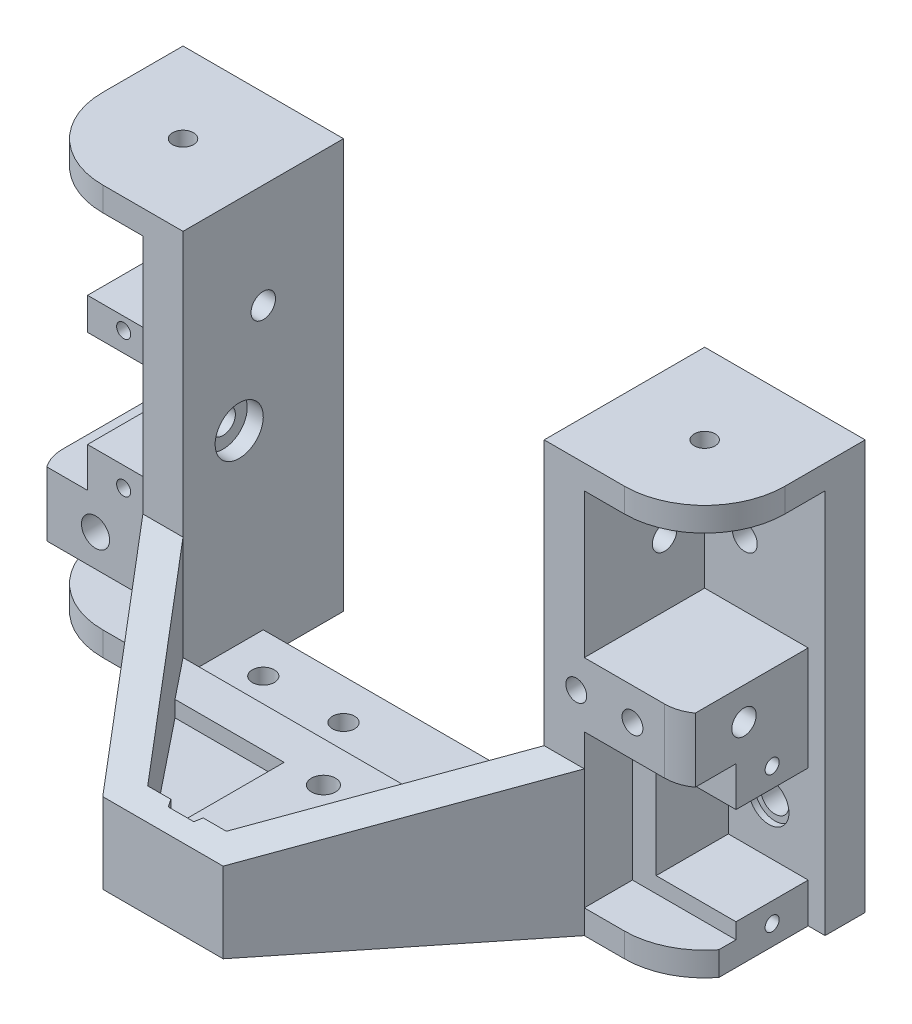
SolidWorks part; units mm, degrees
material "ABS"
ref_plane "Front Plane" through (0, 0, 0) normal (0, 0, 1) x (1, 0, 0)
ref_plane "Top Plane" through (0, 0, 0) normal (0, 1, 0) x (1, 0, 0)
ref_plane "Right Plane" through (0, 0, 0) normal (1, 0, 0) x (0, 0, -1)
sketch "Sketch1" plane through (0, 0, 0) normal (0, 0, 1) x (1, 0, 0)
  line L0 (-22.5, 7) -> (0, 7)
  line L1 (22.5, 7) -> (22.5, 45)
  line L2 (22.5, 45) -> (42.5, 45)
  line L3 (42.5, 45) -> (42.5, 0)
  line L4 (42.5, 0) -> (-42.5, 0)
  line L5 (-42.5, 0) -> (-42.5, 45)
  line L6 (-42.5, 45) -> (-22.5, 45)
  line L7 (-22.5, 45) -> (-22.5, 7)
  line L8 (-35.5, 39.9194) -> (-35.5, 0) construction
  line L9 (35.5, 39.9194) -> (35.5, 0) construction
  line L10 (0, 7) -> (0, 0) construction
  line L14 (0, 7) -> (22.5, 7)
  circle A0 centre (35.5, 8) radius 1.75
  circle A1 centre (-35.5, 8) radius 1.75
  circle A2 centre (32.5, 35) radius 1.55
  circle A3 centre (-32.5, 35) radius 1.55
  point P8 (0, 0)
  dimension "D3" = 3.5
  dimension "D10" = 3.1
  dimension "D1" = 71
  dimension "D2" = 22.5
  dimension "D4" = 8
  dimension "D5" = 7
  dimension "D6" = 7
  dimension "D7" = 45
  dimension "D8" = 35
  dimension "D9" = 3
extrude "main flange" add sketch "Sketch1" along normal blind 5
ref_plane "Plane1" through (22.5, 0, 0) normal (1, 0, 0) x (0, 0, -1)
sketch "Sketch2" plane through (22.5, 0, 0) normal (1, 0, 0) x (0, 0, -1)
  line L0 (-13, 45) -> (-13, 0) construction
  line L1 (-5, 45) -> (-20, 45)
  line L2 (-5, 45) -> (-5, 0)
  line L3 (-5, 0) -> (-20, 0)
  line L4 (-20, 45) -> (-20, 0)
  circle A0 centre (-13, 23) radius 1.525
  circle A1 centre (-10, 35) radius 1.525
  dimension "D2" = 3.05
  dimension "D5" = 3.05
  dimension "D1" = 15
  dimension "D3" = 23
  dimension "D4" = 13
  dimension "D6" = 35
  dimension "D7" = 3
extrude "side flange" add sketch "Sketch2" along normal blind 5
sketch "Sketch8" plane through (22.5, 0, 0) normal (-1, 0, 0) x (0, 0, 1)
  circle A0 centre (13, 23) radius 3
  dimension "D1" = 6
extrude "bearing cutout" [suppressed] cut sketch "Sketch8" against normal blind 2
mirror "Mirror1" about plane through (0, 0, 0) normal (1, 0, 0) of "side flange"
sketch "Sketch11" plane through (0, 0, 0) normal (0, -1, 0) x (1, 0, 0)
  line L0 (27.5, 20) -> (22.5, 20) construction
  line L1 (-42.5, 0) -> (42.5, 0)
  line L2 (-42.5, 0) -> (-42.5, 10)
  line L3 (-32.5, 20) -> (32.5, 20)
  line L4 (42.5, 0) -> (42.5, 10)
  arc A0 (32.5, 20) -> (42.5, 10) centre (32.5, 10) cw
  arc A1 (-42.5, 10) -> (-32.5, 20) centre (-32.5, 10) cw
  circle A2 centre (-32.5, 10) radius 1.3
  circle A3 centre (32.5, 10) radius 1.3
  dimension "D1" = 10
  dimension "D2" = 2.6
extrude "Boss-Extrude3" add sketch "Sketch11" along normal blind 3
sketch "Sketch12" plane through (0, 0, 0) normal (0, 1, 0) x (1, 0, 0)
  line L0 (-4, -3) -> (-4, 0)
  line L1 (22.5, 0) -> (-22.5, 0) construction
  line L2 (-4, 0) -> (4, 0)
  line L3 (4, 0) -> (4, -3)
  line L4 (0, 0) -> (0, -3) construction
  arc A0 (4, -3) -> (-4, -3) centre (0, -3) cw
  circle A1 centre (0, -3) radius 1.5 construction
  dimension "D2" = 8
  dimension "D3" = 3
  dimension "D1" = 3
extrude "Boss-Extrude4" add sketch "Sketch12" along normal up to surface (7 mm away) up to face at (5.625, 7, 3.125)
hole_wizard "CSK for M3 Flat Head Machine Screw1" positions "Sketch14" profile "Sketch15" countersink size "M3" standard "ANSI Metric" end condition up to next
sketch "Sketch14" plane through (0, -3, 0) normal (0, -1, 0) x (-1, 0, 0)
  line L0 (0, -3) -> (0, 0) construction
  point P0 (0, -3)
  dimension "D1" = 3
sketch "Sketch15" plane through (0, -3, 3) normal (1, 0, 0) x (0, 0, -1)
  line L0 (0, 0) -> (0, 10)
  line L1 (0, 10) -> (1.8, 10)
  line L2 (1.8, 10) -> (1.8, 1.5)
  line L3 (1.8, 1.5) -> (3.15, 0.15)
  line L4 (3.15, 0.15) -> (3.15, 0)
  line L6 (3.15, 0) -> (0, 0)
  line L7 (-1.8, 1.5) -> (-3.15, 0.15) construction
  line L11 (0, -6.35) -> (0, 107.95) construction
  dimension "Thru Hole Dia." = 3.6
  dimension "Thru Hole Depth" = 10
  dimension "C'Sink Dia." = 6.3
  dimension "C'Sink Angle" = 90
  dimension "Head Clearance" = 0.15
sketch "Sketch16" plane through (0, 45, 0) normal (0, 1, 0) x (1, 0, 0)
  line L0 (-22.5, 0) -> (-42.5, 0) construction
  line L1 (-42.5, 0) -> (-22.5, 0)
  line L2 (-42.5, 0) -> (-42.5, -10)
  line L3 (-32.5, -20) -> (-22.5, -20)
  line L4 (42.5, 0) -> (42.5, -10)
  line L5 (-42.5, -5) -> (-42.5, 0) construction
  line L6 (42.5, -5) -> (42.5, 0) construction
  line L7 (27.5, -20) -> (22.5, -20) construction
  line L8 (-22.5, 0) -> (-22.5, -20)
  line L9 (-22.5, -20) -> (-22.5, 0) construction
  line L10 (22.5, 0) -> (22.5, -20)
  line L11 (22.5, -20) -> (22.5, 0) construction
  line L12 (22.5, 0) -> (42.5, 0)
  line L13 (22.5, -20) -> (32.5, -20)
  arc A0 (-42.5, -10) -> (-32.5, -20) centre (-32.5, -10) ccw
  arc A1 (32.5, -20) -> (42.5, -10) centre (32.5, -10) ccw
  circle A2 centre (-32.5, -10) radius 1.3
  circle A3 centre (32.5, -10) radius 1.3
  dimension "D1" = 10
  dimension "D2" = 2.6
extrude "Top support" add sketch "Sketch16" along normal blind 3
sketch "Sketch18" plane through (27.5, 0, 0) normal (1, 0, 0) x (0, 0, -1)
  line L0 (-20, 45) -> (-20, 0) construction
  line L1 (-20, 27) -> (-5, 27)
  line L2 (-20, 27) -> (-20, 19)
  line L3 (-20, 19) -> (-5, 19)
  line L4 (-5, 27) -> (-5, 19)
  line L5 (-5, 0) -> (-5, 45) construction
  circle A0 centre (-13, 23) radius 1.525
  circle A1 centre (-13, 23) radius 1.525 construction
  dimension "D1" = 4
  dimension "D2" = 4
extrude "Boss-Extrude5" add sketch "Sketch18" along normal up to surface (15 mm away) up to face at (42.5, 19.6875, 5.9375)
sketch "Sketch19" plane through (0, 0, 5) normal (0, 0, 1) x (1, 0, 0)
  line L0 (-27.5, 45) -> (-27.5, 0) construction
  line L1 (-27.5, 12) -> (-42.5, 12)
  line L2 (-27.5, 12) -> (-27.5, 4)
  line L3 (-27.5, 4) -> (-42.5, 4)
  line L4 (-42.5, 12) -> (-42.5, 4)
  line L5 (-42.5, 45) -> (-42.5, 0) construction
  circle A0 centre (-35.5, 8) radius 1.75
  circle A1 centre (-35.5, 8) radius 1.75 construction
  dimension "D1" = 4
  dimension "D2" = 4
extrude "Boss-Extrude6" add sketch "Sketch19" along normal up to surface (15 mm away) up to face at (8.375, 27.35, 20)
fillet "Fillet1" radius 5 2 edges at (42.5, 23, 20) (-42.5, 8, 20)
hole_wizard "M3x0.5 Tapped Hole1" positions "Sketch21" profile "Sketch20" tap size "M3x0.5" standard "ANSI Metric"
sketch "Sketch21" plane through (-42.5, 0, 0) normal (-1, 0, 0) x (0, 0, 1)
  line L2 (15, 8) -> (4, 8) construction
  line L3 (0, 48) -> (0, -3) construction
  line L5 (15, 4) -> (15, 12) construction
  point P0 (11, 8)
  point P11 (4, 8)
  dimension "D1" = 4
  dimension "D3" = 7
sketch "Sketch20" plane through (-42.5, 8, 11) normal (0, 1, 0) x (0, 0, 1)
  line L0 (0, 0) -> (0, 8.2811)
  line L1 (0, 8.2811) -> (1.3, 7.5)
  line L2 (1.3, 7.5) -> (1.3, 0)
  line L5 (1.3, 0) -> (0, 0)
  line L10 (0, 8.2811) -> (-1.3, 7.5) construction
  line L11 (0, -6.35) -> (0, 107.95) construction
  dimension "Tap Drill Dia." = 2.6
  dimension "Tap Drill Depth" = 7.5
  dimension "Drill Angle" = 118
cosmetic thread "Hole Thread1" parameters "D1"=6, "D2"=3
cosmetic thread "Hole Thread2" parameters "D1"=6, "D2"=3
hole_wizard "M3x0.5 Tapped Hole2" positions "Sketch23" profile "Sketch22" tap size "M3x0.5" standard "ANSI Metric"
sketch "Sketch23" plane through (0, 0, 20) normal (0, 0, 1) x (1, 0, 0)
  line L0 (22.5, 23) -> (33.5, 23) construction
  line L1 (22.5, 48) -> (22.5, 0) construction
  line L5 (33.5, 23) -> (37.5, 23) construction
  line L6 (37.5, 19) -> (37.5, 27) construction
  point P0 (33.5, 23)
  point P2 (26.5, 23)
  dimension "D1" = 4
  dimension "D2" = 7
sketch "Sketch22" plane through (33.5, 23, 20) normal (1, 0, 0) x (0, -1, 0)
  line L0 (0, 0) -> (0, 8.2811)
  line L1 (0, 8.2811) -> (1.3, 7.5)
  line L2 (1.3, 7.5) -> (1.3, 0)
  line L5 (1.3, 0) -> (0, 0)
  line L10 (0, 8.2811) -> (-1.3, 7.5) construction
  line L11 (0, -6.35) -> (0, 107.95) construction
  dimension "Tap Drill Dia." = 2.6
  dimension "Tap Drill Depth" = 7.5
  dimension "Drill Angle" = 118
cosmetic thread "Hole Thread3" parameters "D1"=6, "D2"=3
cosmetic thread "Hole Thread4" parameters "D1"=6, "D2"=3
sketch "Sketch24" plane through (0, 0, 5) normal (0, 0, 1) x (1, 0, 0)
  circle A0 centre (35.5, 8) radius 2.5
  dimension "D1" = 5
extrude "Cut-Extrude1" cut sketch "Sketch24" against normal blind 0.75
sketch "Sketch25" plane through (-27.5, 0, 0) normal (-1, 0, 0) x (0, 0, 1)
  circle A0 centre (13, 23) radius 2.5
  dimension "D1" = 5
extrude "Cut-Extrude2" cut sketch "Sketch25" against normal blind 0.75
sketch "Sketch26" plane through (0, 7, 0) normal (0, 1, 0) x (1, 0, 0)
  line L0 (22.5, 0) -> (-22.5, 0) construction
  line L1 (-15.2, 0) -> (-5.2, 0)
  line L2 (-15.2, 0) -> (-15.2, -2.85)
  line L3 (-15.2, -2.85) -> (-5.2, -2.85)
  line L4 (-5.2, 0) -> (-5.2, -2.85)
  line L5 (0, 0) -> (0, 9.323) construction
  line L6 (5.2, 0) -> (5.2, -2.85)
  line L7 (15.2, -2.85) -> (5.2, -2.85)
  line L8 (15.2, 0) -> (15.2, -2.85)
  line L9 (15.2, 0) -> (5.2, 0)
  dimension "D1" = 5.2
  dimension "D2" = 2.85
  dimension "D3" = 10
extrude "Boss-Extrude7" add sketch "Sketch26" along normal blind 10
sketch "Sketch27" plane through (0, 0, 5) normal (0, 0, 1) x (1, 0, 0)
  line L0 (-27.5, 45) -> (-27.5, 12) construction
  line L1 (-27.5, 38) -> (-42.5, 38)
  line L2 (-27.5, 38) -> (-27.5, 32)
  line L3 (-27.5, 32) -> (-42.5, 32)
  line L4 (-42.5, 38) -> (-42.5, 32)
  line L5 (-42.5, 45) -> (-42.5, 12) construction
  line L6 (0, 0) -> (0, 39.7852) construction
  line L7 (-42.5, 35) -> (-32.5, 35) construction
  line L8 (42.5, 35) -> (32.5, 35) construction
  line L9 (42.5, 38) -> (42.5, 32)
  line L10 (27.5, 32) -> (42.5, 32)
  line L11 (27.5, 38) -> (27.5, 32)
  line L12 (27.5, 38) -> (42.5, 38)
  dimension "D1" = 6
sketch "Sketch30" plane through (0, 0, 0) normal (0, 1, 0) x (1, 0, 0)
  line L0 (-22.5, -20) -> (-22.5, -5) construction
  line L1 (-22.5, -5) -> (-3.4641, -5) construction
  line L2 (3.4641, -5) -> (22.5, -5) construction
  line L3 (22.5, -20) -> (22.5, -5) construction
  line L4 (22.5, -20) -> (-22.5, -20) construction
  line L5 (-22.5, -20) -> (-22.5, -5)
  line L6 (-22.5, -5) -> (-3.4641, -5)
  line L7 (3.4641, -5) -> (22.5, -5)
  line L8 (22.5, -20) -> (22.5, -5)
  line L9 (22.5, -20) -> (-22.5, -20)
  arc A0 (-3.4641, -5) -> (3.4641, -5) centre (0, -3) ccw construction
  arc A1 (-3.4641, -5) -> (3.4641, -5) centre (0, -3) ccw
extrude "Cut-Extrude3" [suppressed] cut sketch "Sketch30" against normal offset from surface (2 mm away) 1
sketch "Sketch31" [suppressed] plane through (0, 7, 0) normal (0, 1, 0) x (1, 0, 0)
  line L0 (22.5, -11) -> (22.5, 11) construction
  line L1 (-15.2, 0) -> (-22.5, 0)
  line L2 (-15.2, 0) -> (-15.2, -5)
  line L3 (-15.2, -5) -> (-22.5, -5)
  line L4 (-22.5, 0) -> (-22.5, -5)
  line L5 (15.2, 0) -> (22.5, 0)
  line L6 (15.2, 0) -> (15.2, -5)
  line L7 (15.2, -5) -> (22.5, -5)
  line L8 (22.5, 0) -> (22.5, -5)
  line L9 (3.4641, -5) -> (22.5, -5) construction
extrude "Cut-Extrude4" [suppressed] cut sketch "Sketch31" against normal blind 7
sketch "Sketch32" plane through (0, 0, 5) normal (0, 0, 1) x (1, 0, 0)
  line L0 (40.4, 14.05) -> (30.45, 14.05)
  line L2 (30.45, 14.05) -> (30.45, 1.95)
  line L3 (30.45, 1.95) -> (40.4, 1.95)
  line L4 (40.4, 1.95) -> (40.4, 0)
  line L5 (40.4, 0) -> (27.5, 0)
  line L6 (27.5, 0) -> (27.5, 19) construction
  line L7 (27.5, 0) -> (42.5, 0) construction
  line L8 (27.5, 0) -> (27.5, 19)
  line L9 (27.5, 19) -> (40.4, 19)
  line L10 (40.4, 19) -> (40.4, 14.05)
  line L11 (35.5, 8) -> (30.45, 8) construction
  line L12 (37.5, 19) -> (27.5, 19) construction
  dimension "D1" = 12.1
  dimension "D2" = 5.05
  dimension "D3" = 4.9
extrude "Motor mount" add sketch "Sketch32" along normal blind 9
sketch "Sketch33" plane through (42.5, 0, 0) normal (1, 0, 0) x (0, 0, -1)
  line L0 (-15, 27) -> (-5, 27) construction
  line L1 (-20, -3) -> (-5, -3)
  line L2 (-20, -3) -> (-20, 27)
  line L3 (-20, 27) -> (-5, 27)
  line L4 (-5, -3) -> (-5, 27)
  line L5 (-20, -3) -> (-5, 27) construction
  line L6 (-20, 27) -> (-5, -3) construction
  line L7 (-5, 0) -> (-5, 19) construction
  line L8 (0, -3) -> (-10, -3) construction
  line L9 (-20, 19) -> (-20, 27) construction
  point P0 (-12.5, 12)
extrude "Cut-Extrude6" cut sketch "Sketch33" against normal up to surface (2.1 mm away) up to face at (40.4, 16.525, 9.5)
sketch "Sketch34" plane through (40.4, 0, 0) normal (1, 0, 0) x (0, 0, -1)
  line L0 (-9.5, 16.5) -> (-9.5, 14.05) construction
  line L1 (-14, 14.05) -> (-5, 14.05) construction
  line L2 (-9.5, 14.05) -> (-9.5, 1.95) construction
  line L3 (-14, 1.95) -> (-5, 1.95) construction
  line L4 (-9.5, 1.95) -> (-9.5, -3) construction
  line L5 (-16.1311, -3) -> (-5, -3) construction
  line L7 (-9.5, 8) -> (-14.7798, 8) construction
  circle A0 centre (-9.5, 16.5) radius 0.875
  circle A1 centre (-9.5, -0.5) radius 0.875
  dimension "D1" = 1.75
  dimension "D2" = 17
  dimension "D3" = 8.5
extrude "Cut-Extrude7" cut sketch "Sketch34" against normal blind 7
sketch "Sketch35" plane through (-27.5, 0, 0) normal (-1, 0, 0) x (0, 0, 1)
  line L0 (13, 23) -> (20, 23) construction
  line L1 (20, 45) -> (20, 12) construction
  line L2 (20, 29.05) -> (7.95, 29.05)
  line L3 (7.95, 29.05) -> (7.95, 16.95)
  line L4 (7.95, 16.95) -> (20, 16.95)
  line L5 (20, 16.95) -> (20, 12)
  line L6 (20, 12) -> (5, 12)
  line L7 (5, 12) -> (5, 33.05)
  line L8 (5, 33.05) -> (20, 33.05)
  line L9 (20, 33.05) -> (20, 29.05)
  line L10 (13, 23) -> (7.95, 23) construction
  dimension "D1" = 5.05
  dimension "D2" = 12.1
  dimension "D3" = 4
extrude "Boss-Extrude9" add sketch "Sketch35" along normal blind 9
sketch "Sketch36" plane through (0, 0, 20) normal (0, 0, 1) x (1, 0, 0)
  line L0 (-42.5, 45) -> (-42.5, 12) construction
  line L1 (-27.5, 33.05) -> (-42.5, 33.05)
  line L2 (-27.5, 33.05) -> (-27.5, 4)
  line L3 (-27.5, 4) -> (-42.5, 4)
  line L4 (-42.5, 33.05) -> (-42.5, 4)
extrude "Cut-Extrude8" cut sketch "Sketch36" against normal blind 2.1
sketch "Sketch37" plane through (0, 0, 17.9) normal (0, 0, 1) x (1, 0, 0)
  line L0 (-32, 16.95) -> (-32, 29.05) construction
  line L1 (-36.5, 16.95) -> (-27.5, 16.95) construction
  line L2 (-27.5, 29.05) -> (-36.5, 29.05) construction
  line L3 (-32, 23) -> (-29.1995, 23) construction
  line L4 (-32, 31.5) -> (-32, 29.05) construction
  circle A0 centre (-32, 31.5) radius 0.875
  circle A1 centre (-32, 14.5) radius 0.875
  dimension "D1" = 1.75
  dimension "D2" = 8.5
  dimension "D3" = 8.5
extrude "Cut-Extrude9" cut sketch "Sketch37" against normal blind 7
sketch "Sketch38" [suppressed] plane through (0, -3, 0) normal (0, -1, 0) x (1, 0, 0)
  line L0 (22.5, -11) -> (22.5, 11) construction
  line L1 (-22.5, 0) -> (22.5, 0)
  line L2 (-22.5, 0) -> (-22.5, 10)
  line L3 (-22.5, 10) -> (22.5, 10)
  line L4 (22.5, 0) -> (22.5, 10)
  line L5 (32.5, 20) -> (-32.5, 20) construction
  dimension "D1" = 10
sketch "Sketch39" plane through (0, -3, 0) normal (0, -1, 0) x (1, 0, 0)
  line L0 (22.5, -2.75) -> (22.5, 2.75) construction
  line L1 (-22.5, 0) -> (22.5, 0)
  line L2 (-22.5, 0) -> (-22.5, 10)
  line L3 (-22.5, 10) -> (22.5, 10)
  line L4 (22.5, 0) -> (22.5, 10)
  line L5 (32.5, 20) -> (-32.5, 20) construction
  dimension "D1" = 10
extrude "Cut-Extrude11" cut sketch "Sketch39" against normal through all
sketch "Sketch40" plane through (0, 0, 0) normal (0, 1, 0) x (1, 0, 0)
  line L0 (0, 0) -> (0, -20) construction
  line L1 (22.5, -20) -> (-22.5, -20) construction
  line L2 (0, -15) -> (-21.4186, -15) construction
  circle A0 centre (-17.5, -15) radius 1.375
  circle A1 centre (-7.5, -15) radius 1.375
  circle A2 centre (7.5, -15) radius 1.375
  circle A3 centre (17.5, -15) radius 1.375
  dimension "D1" = 2.75
  dimension "D2" = 7.5
  dimension "D3" = 10
  dimension "D4" = 5
extrude "Mount Holes" cut sketch "Sketch40" against normal through all
sketch "Sketch41" plane through (-22.5, 0, 0) normal (1, 0, 0) x (0, 0, -1)
  circle A0 centre (-13, 23) radius 3
  dimension "D1" = 6
extrude "Bearing Holder" cut sketch "Sketch41" against normal blind 2
sketch "Sketch42" plane through (0, 0, 0) normal (0, 0, -1) x (-1, 0, 0)
  circle A0 centre (-35.5, 8) radius 3
  dimension "D1" = 6
extrude "Cut-Extrude14" cut sketch "Sketch42" against normal blind 2
sketch "Sketch44" plane through (0, -3, 0) normal (0, -1, 0) x (1, 0, 0)
  line L0 (32.5, 20) -> (-32.5, 20) construction
  line L1 (-7.5, 20) -> (7.5, 20) construction
  line L2 (-7.5, 20) -> (-7.5, 45) construction
  line L3 (-7.5, 45) -> (7.5, 45)
  line L4 (7.5, 20) -> (7.5, 45) construction
  line L5 (0, 45) -> (0, 0) construction
  line L6 (-7.5, 45) -> (-27.5, 20)
  line L7 (7.5, 45) -> (27.5, 20)
  line L8 (-27.5, 20) -> (27.5, 20)
  dimension "D1" = 25
  dimension "D2" = 15
  dimension "D3" = 55
extrude "Boss-Extrude10" add sketch "Sketch44" against normal blind 3
sketch "Sketch45" plane through (0, 0, 0) normal (0, 1, 0) x (1, 0, 0)
  line L0 (-27.5, -20) -> (-7.5, -45)
  line L2 (7.5, -45) -> (-7.5, -45) construction
  line L3 (-4.9, -42) -> (-22.5, -20)
  line L4 (22.5, -20) -> (4.9, -42)
  line L5 (-7.5, -45) -> (7.5, -45)
  line L6 (7.5, -45) -> (27.5, -20)
  line L8 (22.5, -20) -> (27.5, -20)
  line L9 (-27.5, -20) -> (-22.5, -20)
  line L10 (-22.5, -20) -> (-22.6142, -20.1928)
  line L11 (-4.9, -42) -> (4.9, -42)
  dimension "D1" = 3
extrude "Boss-Extrude11" add sketch "Sketch45" along normal blind 15
sketch "Sketch46" plane through (0, 0, 0) normal (1, 0, 0) x (0, 0, -1)
  line L0 (-20, 15) -> (-45, 7)
  line L1 (-45, 15) -> (-45, -3) construction
  line L2 (-45, 7) -> (-45, 15)
  line L3 (-45, 15) -> (-20, 15)
  line L4 (-20, -3) -> (-45, -3) construction
  dimension "D1" = 10
extrude "Cut-Extrude15" cut sketch "Sketch46" against normal through all both and the other way through all
sketch "Sketch50" plane through (0, 0, 0) normal (0, 1, 0) x (1, 0, 0)
  line L0 (-22.5, -20) -> (22.5, -20)
  line L1 (22.5, -24.75) -> (22.5, 24.75) construction
  line L2 (22.5, -20) -> (18.5, -25)
  line L3 (4.9, -42) -> (22.5, -20) construction
  line L4 (18.5, -25) -> (4.9, -25)
  line L5 (4.9, -25) -> (4.9, -42)
  line L6 (4.9, -42) -> (-4.9, -42)
  line L7 (-4.9, -42) -> (-4.9, -25)
  line L8 (-4.9, -25) -> (-18.5, -25)
  line L9 (-22.5, -20) -> (-4.9, -42) construction
  line L10 (-18.5, -25) -> (-22.5, -20)
  dimension "D1" = 5
extrude "Boss-Extrude12" add sketch "Sketch50" along normal blind 2
sketch "Sketch48" plane through (0, -3, 0) normal (0, -1, 0) x (1, 0, 0)
  line L0 (0, 45) -> (0, 10) construction
  line L1 (7.5, 45) -> (-7.5, 45) construction
  line L2 (22.5, 10) -> (-22.5, 10) construction
  circle A0 centre (0, 40) radius 1.5
  circle A1 centre (0, 25) radius 1.5
  dimension "D2" = 3
  dimension "D1" = 15
  dimension "D3" = 5
extrude "Cut-Extrude16" cut sketch "Sketch48" against normal up to next
sketch "Sketch51" plane through (0, 2, 0) normal (0, 1, 0) x (1, 0, 0)
  line L1 (3.1754, -40) -> (1.5877, -37.25)
  line L2 (1.5877, -37.25) -> (-1.5877, -37.25)
  line L3 (-1.5877, -37.25) -> (-3.1754, -40)
  line L4 (-3.1754, -40) -> (-1.5877, -42.75)
  line L5 (-1.5877, -42.75) -> (1.5877, -42.75)
  line L6 (1.5877, -42.75) -> (3.1754, -40)
  circle A0 centre (0, -40) radius 2.75 construction
  dimension "D1" = 5.5
extrude "Cut-Extrude17" cut sketch "Sketch51" along normal through all
equation "\"clearance\"= 0.2mm'3D printed hole"
equation "\"tight\"= - 0.2mm'3D printed hole"
